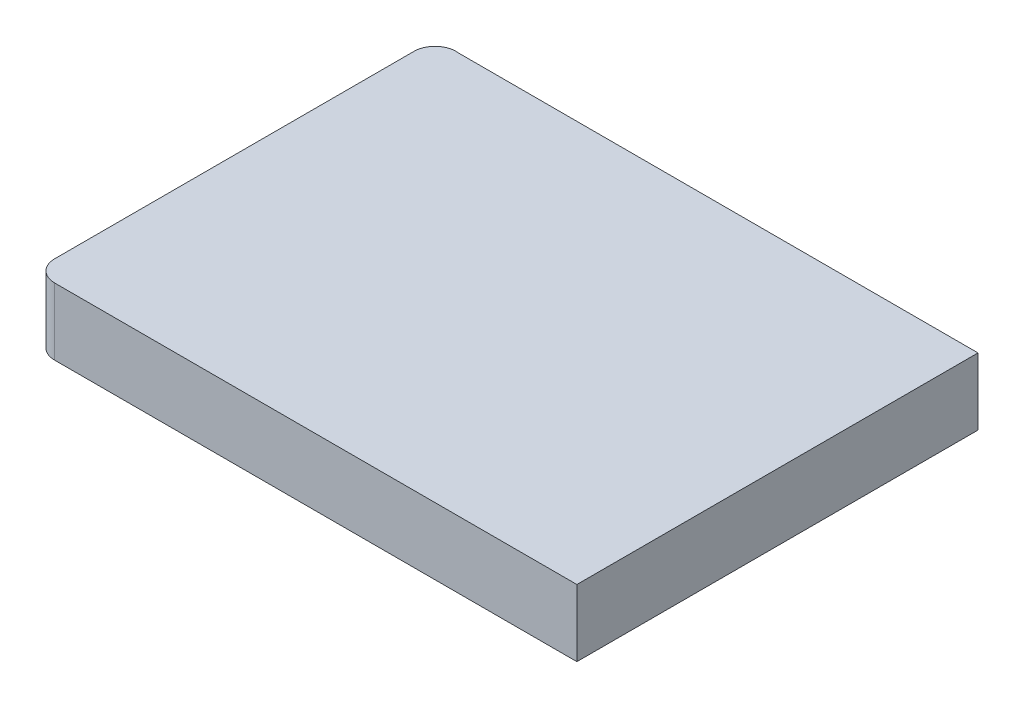
SolidWorks part; units mm, degrees
ref_plane "Alzado" through (0, 0, 0) normal (0, 0, 1) x (1, 0, 0)
ref_plane "Planta" through (0, 0, 0) normal (0, 1, 0) x (1, 0, 0)
ref_plane "Vista lateral" through (0, 0, 0) normal (1, 0, 0) x (0, 0, -1)
sketch "Croquis1" plane through (0, 0, 0) normal (0, 1, 0) x (1, 0, 0)
  line L2 (35.2751, -17.3628) -> (35.2751, 30.6372)
  line L3 (35.2751, 30.6372) -> (-26.9256, 30.6372)
  line L6 (35.2751, -17.3628) -> (-27.2249, -17.3628)
  line L7 (-29.7249, -14.8628) -> (-29.7249, 28.1552)
  arc A3 (-27.2249, -17.3628) -> (-29.7249, -14.8628) centre (-27.2249, -14.8628) cw
  arc A4 (-29.7249, 28.1552) -> (-26.9256, 30.6372) centre (-27.2249, 28.1552) cw
  dimension "D2" = 2.5
  dimension "D3" = 48
  dimension "D1" = 65
extrude "Saliente-Extruir1" add sketch "Croquis1" along normal blind 8
